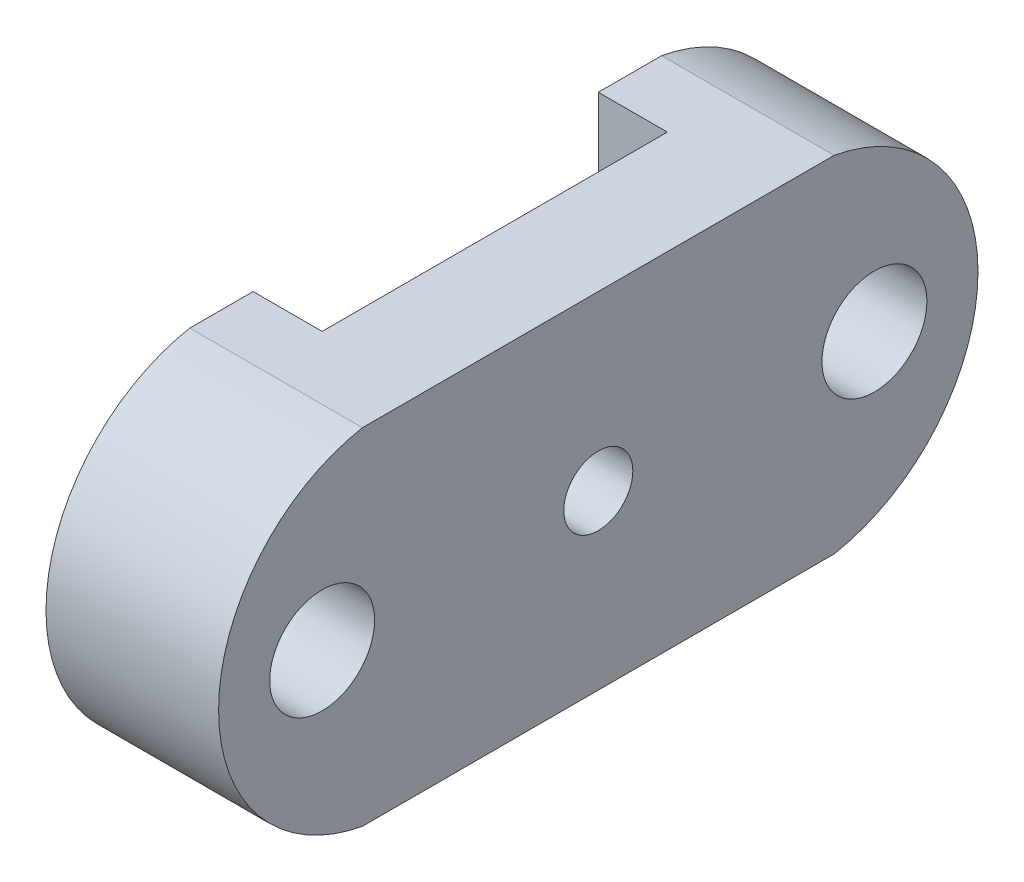
SolidWorks part; units mm, degrees
ref_plane "Front Plane" through (0, 0, 0) normal (0, 0, 1) x (1, 0, 0)
ref_plane "Top Plane" through (0, 0, 0) normal (0, 1, 0) x (1, 0, 0)
ref_plane "Right Plane" through (0, 0, 0) normal (1, 0, 0) x (0, 0, -1)
sketch "Sketch1" plane through (0, 0, 0) normal (1, 0, 0) x (0, 0, -1)
  line L1 (55, -25) -> (-55, -25)
  line L2 (55, -25) -> (55, 25)
  line L3 (55, 25) -> (-55, 25)
  line L4 (-55, -25) -> (-55, 25)
  line L5 (55, -25) -> (-55, 25) construction
  line L6 (55, 25) -> (-55, -25) construction
  point P0 (0, 0)
  dimension "D1" = 50
  dimension "D2" = 110
extrude "Boss-Extrude1" add sketch "Sketch1" along normal blind 25 contours L4 L3 L2 L1
sketch "Sketch2" plane through (25, 0, 0) normal (1, 0, 0) x (0, 0, -1)
  circle A0 centre (-40, -0.0069) radius 7.6
  circle A1 centre (40, -0.0069) radius 7.6
  dimension "D1" = 15.2
  dimension "D2" = 15.2
extrude "Cut-Extrude1" cut sketch "Sketch2" against normal through all
hole_wizard "M8 Clearance Hole1" positions "Sketch3" profile "Sketch4" hole size "M8" standard "ANSI Metric"
sketch "Sketch3" plane through (25, 0, 0) normal (1, 0, 0) x (0, 0, -1)
  point P0 (0, 0)
sketch "Sketch4" plane through (25, 0, 0) normal (0, 1, 0) x (0, 0, -1)
  line L0 (0, 0) -> (0, 28.0043)
  line L1 (0, 28.0043) -> (5, 25)
  line L2 (5, 25) -> (5, 0)
  line L5 (5, 0) -> (0, 0)
  line L10 (0, 28.0043) -> (-5, 25) construction
  line L11 (0, -6.35) -> (0, 107.95) construction
  dimension "Hole Dia." = 10
  dimension "Hole Depth" = 25
  dimension "Drill Angle" = 118
sketch "Sketch5" plane through (0, -25, 0) normal (0, -1, 0) x (1, 0, 0)
  line L0 (0, -25) -> (10, -25)
  line L3 (0, -55) -> (0, 55) construction
  line L4 (10, -25) -> (10, 25)
  line L5 (10, 25) -> (0, 25)
  line L6 (0, 25) -> (0, -25)
  line L7 (25, -55) -> (25, 55) construction
  line L8 (25, 55) -> (0, 55) construction
  line L9 (25, -55) -> (0, -55) construction
  dimension "D1" = 15
  dimension "D2" = 30
  dimension "D3" = 30
extrude "Cut-Extrude2" cut sketch "Sketch5" against normal through all
sketch "Sketch6" plane through (10, 0, 0) normal (-1, 0, 0) x (0, 0, 1)
  line L1 (6.5, 7.5) -> (-6.5, 7.5)
  line L2 (6.5, 7.5) -> (6.5, -7.5)
  line L3 (6.5, -7.5) -> (-6.5, -7.5)
  line L4 (-6.5, 7.5) -> (-6.5, -7.5)
  line L5 (6.5, 7.5) -> (-6.5, -7.5) construction
  line L6 (6.5, -7.5) -> (-6.5, 7.5) construction
  point P0 (0, 0)
  dimension "D1" = 13
  dimension "D2" = 15
extrude "Cut-Extrude3" cut sketch "Sketch6" against normal blind 6.8
sketch "Sketch7" plane through (0, 0, 0) normal (-1, 0, 0) x (0, 0, 1)
  line L0 (-25, -25) -> (-25.9958, -36.3674)
  line L1 (-25.9958, -36.3674) -> (-60.7802, -28.6926)
  line L2 (-60.7802, -28.6926) -> (-59.2947, 34.5629)
  line L3 (-59.2947, 34.5629) -> (-23.2604, 33.7167)
  line L4 (-23.2604, 33.7167) -> (-25, 25)
  line L5 (25, -25) -> (27.2312, -36.3674)
  line L6 (27.2312, -36.3674) -> (50.6196, -36.3674)
  line L7 (50.6196, -36.3674) -> (65.9081, -26.5226)
  line L8 (65.9081, -26.5226) -> (65.9081, 30.4802)
  line L9 (65.9081, 30.4802) -> (20.4476, 40.5038)
  line L10 (20.4476, 40.5038) -> (25, 25)
  arc A0 (-25, -25) -> (-25, 25) centre (-29.5833, 0) cw
  arc A1 (25, -25) -> (25, 25) centre (29.5833, 0) ccw
extrude "Cut-Extrude4" cut sketch "Sketch7" against normal up to surface (25 mm away) up to face at (25, 0, -5)
hole_wizard "Tap Drill for M3x0.5 Tap1" positions "Sketch9" profile "Sketch10" hole size "M3x0.5" standard "ANSI Metric"
sketch "Sketch9" plane through (0, -25, 0) normal (0, -1, 0) x (-1, 0, 0)
  line L3 (0, 25) -> (-10, 25) construction
  line L4 (-10, -25) -> (0, -25) construction
  point P0 (-16.9848, 19)
  point P2 (-16.9848, -19)
  dimension "D1" = 38
  dimension "D2" = 6
  dimension "D3" = 6
sketch "Sketch10" plane through (16.9848, -25, -19) normal (1, 0, 0) x (0, 0, -1)
  line L0 (0, 0) -> (0, 33.2511)
  line L1 (0, 33.2511) -> (1.25, 32.5)
  line L2 (1.25, 32.5) -> (1.25, 0)
  line L5 (1.25, 0) -> (0, 0)
  line L10 (0, 33.2511) -> (-1.25, 32.5) construction
  line L11 (0, -6.35) -> (0, 107.95) construction
  dimension "Hole Dia." = 2.5
  dimension "Hole Depth" = 32.5
  dimension "Drill Angle" = 118
